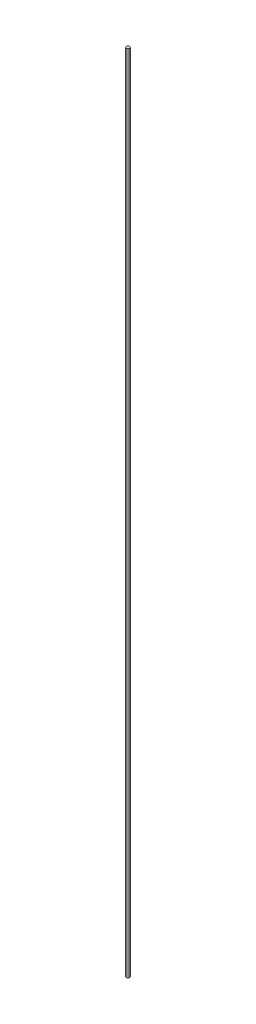
SolidWorks part; units mm, degrees
ref_plane "Front Plane" through (0, 0, 0) normal (0, 0, 1) x (1, 0, 0)
ref_plane "Top Plane" through (0, 0, 0) normal (0, 1, 0) x (1, 0, 0)
ref_plane "Right Plane" through (0, 0, 0) normal (1, 0, 0) x (0, 0, -1)
sketch "Sketch1" plane through (0, 0, 0) normal (0, 1, 0) x (1, 0, 0)
  circle A0 centre (0, 0) radius 0.3225
  dimension "D1" = 0.645
extrude "Boss-Extrude1" add sketch "Sketch1" along normal blind 155
